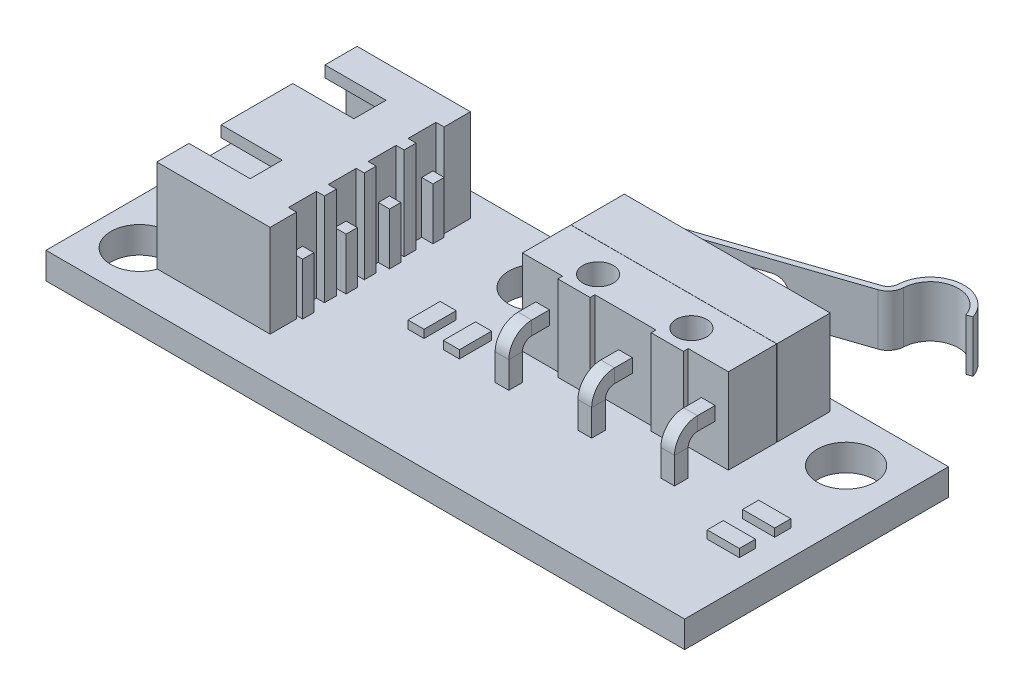
SolidWorks part; units mm, degrees
ref_plane "Front Plane" through (0, 0, 0) normal (0, 0, 1) x (1, 0, 0)
ref_plane "Top Plane" through (0, 0, 0) normal (0, 1, 0) x (1, 0, 0)
ref_plane "Right Plane" through (0, 0, 0) normal (1, 0, 0) x (0, 0, -1)
sketch "Sketch1" plane through (0, 0, 0) normal (0, 1, 0) x (1, 0, 0)
  line L1 (-19.85, -8.2) -> (19.85, -8.2)
  line L2 (-19.85, -8.2) -> (-19.85, 8.2)
  line L3 (-19.85, 8.2) -> (19.85, 8.2)
  line L4 (19.85, -8.2) -> (19.85, 8.2)
  line L5 (-19.85, -8.2) -> (19.85, 8.2) construction
  line L6 (-19.85, 8.2) -> (19.85, -8.2) construction
  point P0 (0, 0)
  dimension "D1" = 39.7
  dimension "D2" = 16.4
extrude "Boss-Extrude1" add sketch "Sketch1" along normal blind 1.65
sketch "Sketch2" plane through (0, 1.65, 0) normal (0, 1, 0) x (1, 0, 0)
  line L0 (19.85, -8.2) -> (19.85, 8.2) construction
  line L1 (13.2, 7.5) -> (0.4, 7.5)
  line L2 (13.2, 7.5) -> (13.2, 0.87)
  line L3 (13.2, 0.87) -> (0.4, 0.87)
  line L4 (0.4, 7.5) -> (0.4, 0.87)
  line L5 (19.85, 8.2) -> (-19.85, 8.2) construction
  dimension "D1" = 6.65
  dimension "D2" = 12.8
  dimension "D3" = 0.7
  dimension "D4" = 6.63
extrude "Boss-Extrude2" add sketch "Sketch2" along normal blind 5.3
sketch "Sketch3" plane through (0, 6.95, 0) normal (0, 1, 0) x (1, 0, 0)
  line L0 (0.4, 0.87) -> (13.2, 0.87) construction
  line L1 (0.4, 0.87) -> (2.9, 0.87)
  line L2 (0.4, 0.87) -> (0.4, 1.17)
  line L3 (0.4, 1.17) -> (2.9, 1.17)
  line L4 (2.9, 0.87) -> (2.9, 1.17)
  line L5 (4.9, 0.87) -> (8.7, 0.87)
  line L6 (4.9, 0.87) -> (4.9, 1.17)
  line L7 (4.9, 1.17) -> (8.7, 1.17)
  line L8 (8.7, 0.87) -> (8.7, 1.17)
  line L9 (0.4, 7.5) -> (0.4, 0.87) construction
  line L10 (13.2, 0.87) -> (10.7, 0.87)
  line L11 (13.2, 0.87) -> (13.2, 1.17)
  line L12 (13.2, 1.17) -> (10.7, 1.17)
  line L13 (10.7, 0.87) -> (10.7, 1.17)
  line L14 (0.4, 4.185) -> (13.2, 4.185)
  line L15 (0.4, 4.185) -> (0.4, 4.175)
  line L16 (0.4, 4.175) -> (13.2, 4.175)
  line L17 (13.2, 4.185) -> (13.2, 4.175)
  line L18 (13.2, 0.87) -> (13.2, 7.5) construction
  point P24 (6.8, 0.87)
  point P26 (6.8, 1.17)
  dimension "D1" = 0.01
  dimension "D2" = 3.8
  dimension "D3" = 0.3
  dimension "D4" = 2
  dimension "D5" = 2
extrude "Cut-Extrude1" cut sketch "Sketch3" against normal up to surface (5.3 mm away) up to face at (0, 1.65, 0)
sketch "Sketch4" plane through (0, 6.95, 0) normal (0, 1, 0) x (1, 0, 0)
  line L0 (2.9, 0.87) -> (4.9, 0.87) construction
  line L1 (8.7, 0.87) -> (10.7, 0.87) construction
  circle A0 centre (3.9, 2.37) radius 0.95
  circle A1 centre (9.7, 2.37) radius 0.95
  point P6 (3.9, 0.87)
  point P9 (9.7, 0.87)
  dimension "D1" = 1.9
  dimension "D2" = 1.5
extrude "Cut-Extrude2" cut sketch "Sketch4" against normal up to surface (5.3 mm away) up to face at (6.8, 1.65, -5.8425)
sketch "Sketch5" plane through (0, 6.95, 0) normal (0, 1, 0) x (1, 0, 0)
  line L0 (4.4, 7.5) -> (4.4, 7.75) construction
  line L1 (13.2, 7.5) -> (0.4, 7.5) construction
  line L2 (3.65, 7.5) -> (3.65, 7.75)
  line L3 (5.15, 7.5) -> (5.15, 7.75)
  line L4 (0.4, 7.5) -> (0.4, 4.185) construction
  line L5 (13.2, 7.5) -> (0.4, 7.5) construction
  arc A0 (3.65, 7.5) -> (5.15, 7.5) centre (4.4, 7.5) ccw
  arc A1 (5.15, 7.75) -> (3.65, 7.75) centre (4.4, 7.75) ccw
  point P4 (4.4, 7.625)
  point P11 (4.4, 8.5)
  dimension "D1" = 4
  dimension "D2" = 1
  dimension "D3" = 1.5
extrude "Boss-Extrude3" add sketch "Sketch5" against normal blind 3 from offset 1.1 offset against normal yes
sketch "Sketch6" plane through (0, 6.95, 0) normal (0, 1, 0) x (1, 0, 0)
  line L0 (1.3031, 7.5) -> (12.4306, 11.2413)
  line L1 (13.2, 7.5) -> (0.4, 7.5) construction
  line L2 (13.2, 11.5) -> (16.5175, 12.6154) construction
  line L3 (13.2, 4.185) -> (13.2, 7.5) construction
  line L5 (1.3031, 7.5) -> (0.8291, 7.3407)
  arc A0 (16.5175, 12.6154) -> (13.1108, 12.1414) centre (14.8588, 12.0577) ccw
  arc A1 (5.15, 7.75) -> (3.65, 7.75) centre (4.4, 7.75) ccw construction
  arc A2 (12.4306, 11.2413) -> (13.1108, 12.1414) centre (12.1119, 12.1892) ccw
  dimension "D2" = 1.75
  dimension "D3" = 1
  dimension "D1" = 4
  dimension "D4" = 0.5
extrude "Extrude-Thin1" add sketch "Sketch6" against normal blind 3.2 from offset 1 separate body thin thin type one direction wall 0.35 offset against normal yes
sketch "Sketch7" plane through (0, 1.65, 0) normal (0, 1, 0) x (1, 0, 0)
  line L0 (-19.85, -8.2) -> (19.85, -8.2) construction
  line L1 (-15.41, 6.7) -> (-8.37, 6.7)
  line L2 (-15.41, 6.7) -> (-15.41, -5.75)
  line L3 (-15.41, -5.75) -> (-8.37, -5.75)
  line L4 (-8.37, 6.7) -> (-8.37, -5.75)
  line L6 (-19.85, 8.2) -> (-19.85, -8.2) construction
  dimension "D1" = 2.45
  dimension "D2" = 12.45
  dimension "D3" = 7.04
  dimension "D4" = 4.44
extrude "Boss-Extrude4" add sketch "Sketch7" along normal blind 5.75
sketch "Sketch8" plane through (0, 0, 0) normal (0, -1, 0) x (1, 0, 0)
  line L0 (19.85, 8.2) -> (19.85, -8.2) construction
  line L1 (19.85, -8.2) -> (-19.85, -8.2) construction
  line L2 (-19.85, -8.2) -> (-19.85, 8.2) construction
  circle A0 centre (16.6125, -5.0725) radius 1.7875
  circle A1 centre (-2.5625, -5.0725) radius 1.7875
  circle A2 centre (-17.0625, -5.6125) radius 1.7875
  circle A3 centre (-17.0625, 5.1625) radius 1.7875
  point P8 (16.6125, -6.86)
  point P9 (18.4, -5.0725)
  point P10 (-2.5625, -6.86)
  point P11 (-4.35, -5.0725)
  point P12 (-17.0625, -7.4)
  point P13 (-18.85, -5.6125)
  point P14 (-18.85, 5.1625)
  point P15 (-17.0625, 6.95)
  point P20 (14.825, -5.0725)
  point P21 (-0.775, -5.0725)
  point P24 (-17.0625, 3.375)
  point P25 (-17.0625, -3.825)
  dimension "D1" = 3.575
  dimension "D2" = 1.45
  dimension "D3" = 1.34
  dimension "D4" = 15.6
  dimension "D5" = 0.8
  dimension "D6" = 1
  dimension "D7" = 7.2
extrude "Cut-Extrude3" cut sketch "Sketch8" against normal up to surface (1.65 mm away) up to face at (6.8, 1.65, -1.5708)
sketch "Sketch10" plane through (-15.41, 0, 0) normal (-1, 0, 0) x (0, 0, 1)
  line L0 (5.75, 7.4) -> (5.75, 1.65) construction
  line L1 (-6, 2.35) -> (5.05, 2.35)
  line L2 (-6, 2.35) -> (-6, 6.7)
  line L3 (-6, 6.7) -> (5.05, 6.7)
  line L4 (5.05, 2.35) -> (5.05, 6.7)
  line L5 (-6, 2.35) -> (5.05, 6.7) construction
  line L6 (-6, 6.7) -> (5.05, 2.35) construction
  line L7 (-6.7, 7.4) -> (5.75, 7.4) construction
  line L8 (-6.7, 7.4) -> (-6.7, 1.65) construction
  point P0 (-0.475, 4.525)
  point P9 (-0.475, 7.4)
  point P12 (-6.7, 4.525)
  dimension "D1" = 0.7
  dimension "D2" = 0.7
extrude "Cut-Extrude4" cut sketch "Sketch10" against normal offset from surface (6.04 mm away) 1 up to face at (-8.37, 4.525, -0.475)
sketch "Sketch11" plane through (0, 7.4, 0) normal (0, 1, 0) x (1, 0, 0)
  line L0 (-15.41, 4.931) -> (-15.41, -4.481) construction
  line L1 (-15.41, 4.7) -> (-11.61, 4.7)
  line L2 (-15.41, 4.7) -> (-15.41, 2.7)
  line L3 (-15.41, 2.7) -> (-11.61, 2.7)
  line L4 (-11.61, 4.7) -> (-11.61, 2.7)
  line L5 (-15.3743, -5.75) -> (-8.37, -5.75) construction
  line L6 (-15.41, -1.75) -> (-11.61, -1.75)
  line L7 (-15.41, -1.75) -> (-15.41, -3.75)
  line L8 (-15.41, -3.75) -> (-11.61, -3.75)
  line L9 (-11.61, -1.75) -> (-11.61, -3.75)
  line L10 (-8.37, 6.7) -> (-15.41, 6.7) construction
  dimension "D1" = 2
  dimension "D2" = 2
  dimension "D3" = 2
  dimension "D4" = 3.8
extrude "Cut-Extrude5" cut sketch "Sketch11" against normal up to next (0.7 mm away)
sketch "Sketch12" plane through (-9.37, 0, 0) normal (-1, 0, 0) x (0, 0, 1)
  line L0 (-6, 4.525) -> (5.05, 4.525) construction
  line L1 (-4.875, 4.875) -> (-4.175, 4.875)
  line L2 (-4.875, 4.875) -> (-4.875, 4.175)
  line L3 (-4.875, 4.175) -> (-4.175, 4.175)
  line L4 (-4.175, 4.875) -> (-4.175, 4.175)
  line L5 (-2.175, 4.875) -> (-1.475, 4.875)
  line L6 (-2.175, 4.875) -> (-2.175, 4.175)
  line L7 (-2.175, 4.175) -> (-1.475, 4.175)
  line L8 (-1.475, 4.875) -> (-1.475, 4.175)
  line L9 (0.525, 4.875) -> (1.225, 4.875)
  line L10 (0.525, 4.875) -> (0.525, 4.175)
  line L11 (0.525, 4.175) -> (1.225, 4.175)
  line L12 (1.225, 4.875) -> (1.225, 4.175)
  line L13 (3.225, 4.875) -> (3.925, 4.875)
  line L14 (3.225, 4.875) -> (3.225, 4.175)
  line L15 (3.225, 4.175) -> (3.925, 4.175)
  line L16 (3.925, 4.875) -> (3.925, 4.175)
  line L17 (-6, 2.35) -> (-6, 6.7) construction
  line L18 (5.05, 2.35) -> (5.05, 6.7) construction
  line L19 (-1.475, 4.875) -> (0.525, 4.875) construction
  line L20 (-0.475, 4.525) -> (-0.475, 4.875) construction
  line L21 (-2.175, 4.875) -> (-4.175, 4.875) construction
  line L22 (3.225, 4.875) -> (1.225, 4.875) construction
  point P22 (3.225, 4.525)
  dimension "D1" = 0.7
  dimension "D2" = 2
extrude "Boss-Extrude5" add sketch "Sketch12" along normal blind 4
chamfer "Chamfer1" distance 0.2 angle 45 16 edges at (-13.37, 4.875, 3.575) (-13.37, 4.525, 3.925) (-13.37, 4.175, 3.575) (-13.37, 4.525, 3.225) (-13.37, 4.875, 0.875) (-13.37, 4.525, 1.225) (-13.37, 4.175, 0.875) (-13.37, 4.525, 0.525) (-13.37, 4.875, -1.825) (-13.37, 4.525, -1.475) (-13.37, 4.175, -1.825) (-13.37, 4.525, -2.175) (-13.37, 4.875, -4.525) (-13.37, 4.525, -4.175) (-13.37, 4.175, -4.525) (-13.37, 4.525, -4.875)
sketch "Sketch14" plane through (0, 7.4, 0) normal (0, 1, 0) x (1, 0, 0)
  line L0 (-8.37, -5.75) -> (-8.37, 6.7) construction
  line L1 (-8.37, 5.06) -> (-8.87, 5.06)
  line L2 (-8.37, 5.06) -> (-8.37, 3.3225)
  line L3 (-8.37, 3.3225) -> (-8.87, 3.3225)
  line L4 (-8.87, 5.06) -> (-8.87, 3.3225)
  line L5 (-15.41, -5.75) -> (-8.37, -5.75) construction
  line L6 (-8.37, 2.5825) -> (-8.87, 2.5825)
  line L7 (-8.37, 2.5825) -> (-8.37, 0.845)
  line L8 (-8.37, 0.845) -> (-8.87, 0.845)
  line L9 (-8.87, 2.5825) -> (-8.87, 0.845)
  line L10 (-8.37, 0.105) -> (-8.87, 0.105)
  line L11 (-8.37, 0.105) -> (-8.37, -1.6325)
  line L12 (-8.37, -1.6325) -> (-8.87, -1.6325)
  line L13 (-8.87, 0.105) -> (-8.87, -1.6325)
  line L14 (-8.37, -2.3725) -> (-8.87, -2.3725)
  line L15 (-8.37, -2.3725) -> (-8.37, -4.11)
  line L16 (-8.37, -4.11) -> (-8.87, -4.11)
  line L17 (-8.87, -2.3725) -> (-8.87, -4.11)
  line L18 (-8.37, 6.7) -> (-15.41, 6.7) construction
  dimension "D1" = 1.64
  dimension "D2" = 1.64
  dimension "D3" = 0.74
  dimension "D4" = 0.74
  dimension "D5" = 0.74
  dimension "D6" = 0.5
extrude "Cut-Extrude6" cut sketch "Sketch14" against normal up to surface (5.75 mm away) up to face at (-2.5625, 1.65, -6.86)
sketch "Sketch16" plane through (0, 0, -1.17) normal (0, 0, 1) x (1, 0, 0)
  line L0 (0.4, 4.3) -> (1.225, 4.3) construction
  line L1 (1.225, 4.725) -> (2.075, 4.725)
  line L2 (1.225, 4.725) -> (1.225, 3.875)
  line L3 (1.225, 3.875) -> (2.075, 3.875)
  line L4 (2.075, 4.725) -> (2.075, 3.875)
  line L5 (6.375, 4.725) -> (7.225, 4.725)
  line L6 (6.375, 4.725) -> (6.375, 3.875)
  line L7 (6.375, 3.875) -> (7.225, 3.875)
  line L8 (7.225, 4.725) -> (7.225, 3.875)
  line L9 (11.525, 4.725) -> (12.375, 4.725)
  line L10 (11.525, 4.725) -> (11.525, 3.875)
  line L11 (11.525, 3.875) -> (12.375, 3.875)
  line L12 (12.375, 4.725) -> (12.375, 3.875)
  line L13 (0.4, 1.65) -> (0.4, 6.95) construction
  line L14 (1.65, 4.725) -> (1.65, 6.95) construction
  line L15 (2.9, 6.95) -> (0.4, 6.95) construction
  line L16 (11.95, 4.725) -> (11.95, 6.95) construction
  line L17 (13.2, 6.95) -> (10.7, 6.95) construction
  line L18 (6.8, 4.725) -> (6.8, 6.95) construction
  line L19 (8.7, 6.95) -> (4.9, 6.95) construction
  point P20 (6.375, 4.3)
  point P21 (11.525, 4.3)
  dimension "D1" = 0.85
sketch "Sketch17" plane through (2.9, 0, 0) normal (-1, 0, 0) x (0, 0, 1)
  line L0 (-1.17, 4.3) -> (-0.07, 4.3)
  line L1 (-1.17, 4.725) -> (-1.17, 3.875) construction
  line L2 (0.93, 3.3) -> (0.93, 1.65)
  line L3 (8.2, 1.65) -> (-8.2, 1.65) construction
  arc A0 (-0.07, 4.3) -> (0.93, 3.3) centre (-0.07, 3.3) cw
  point P9 (0.93, 4.3)
  dimension "D2" = 1
  dimension "D1" = 2.1
sweep "Sweep1" add profiles "Sketch16" path "Sketch17"
sketch "Sketch18" plane through (-2.2447, 0, -6.6764) normal (-0.3187, 0, -0.9479) x (-0.9479, 0, 0.3187)
  line L0 (-3.1253, 4.35) -> (-10.1253, 4.35) construction
  line L1 (-3.1253, 2.75) -> (-3.1253, 5.95) construction
  line L2 (-3.1253, 3.5) -> (-10.1253, 3.5)
  line L3 (-3.1253, 5.2) -> (-10.1253, 5.2)
  line L4 (-3.1253, 5.2) -> (-3.1253, 3.5)
  arc A1 (-10.1253, 5.2) -> (-10.1253, 3.5) centre (-10.1253, 4.35) ccw
  point P4 (-6.6, 4.35)
  dimension "D1" = 1.7
  dimension "D2" = 7
extrude "Cut-Extrude7" cut sketch "Sketch18" against normal up to surface (0.35 mm away) up to face at (6.6299, 4.35, -9.291)
sketch "Sketch19" plane through (-8.87, 0, 0) normal (1, 0, 0) x (0, 0, -1)
  line L0 (4.875, 4.875) -> (4.675, 4.675) construction
  line L1 (-3.925, 4.875) -> (-3.225, 4.875)
  line L2 (-3.925, 4.875) -> (-3.925, -2)
  line L3 (-3.925, -2) -> (-3.225, -2)
  line L4 (-3.225, 4.875) -> (-3.225, -2)
  line L5 (-1.225, 4.875) -> (-0.525, 4.875)
  line L6 (-1.225, 4.875) -> (-1.225, -2)
  line L7 (-1.225, -2) -> (-0.525, -2)
  line L8 (-0.525, 4.875) -> (-0.525, -2)
  line L9 (1.475, 4.875) -> (2.175, 4.875)
  line L10 (1.475, 4.875) -> (1.475, -2)
  line L11 (1.475, -2) -> (2.175, -2)
  line L12 (2.175, 4.875) -> (2.175, -2)
  line L13 (4.175, 4.875) -> (4.875, 4.875)
  line L14 (4.175, 4.875) -> (4.175, -2)
  line L15 (4.175, -2) -> (4.875, -2)
  line L16 (4.875, 4.875) -> (4.875, -2)
  line L17 (4.875, 4.875) -> (4.875, 4.175) construction
  line L18 (2.175, 4.875) -> (2.175, 4.175) construction
  line L19 (1.475, 4.875) -> (2.175, 4.875) construction
  line L20 (-0.525, 4.875) -> (-0.525, 4.175) construction
  line L21 (-0.525, 4.875) -> (-0.725, 4.675) construction
  line L22 (-3.225, 4.875) -> (-3.225, 4.175) construction
  line L23 (-3.225, 4.875) -> (-3.425, 4.675) construction
  line L24 (-6.95, 0) -> (-3.375, 0) construction
  dimension "D1" = 2
extrude "Boss-Extrude6" add sketch "Sketch19" along normal blind 0.7
sketch "Sketch20" plane through (0, 0, 0) normal (0, -1, 0) x (1, 0, 0)
  line L1 (1.225, 1.355) -> (2.075, 1.355)
  line L2 (1.225, 1.355) -> (1.225, 0.505)
  line L3 (1.225, 0.505) -> (2.075, 0.505)
  line L4 (2.075, 1.355) -> (2.075, 0.505)
  line L5 (6.375, 1.355) -> (7.225, 1.355)
  line L6 (6.375, 1.355) -> (6.375, 0.505)
  line L7 (6.375, 0.505) -> (7.225, 0.505)
  line L8 (7.225, 1.355) -> (7.225, 0.505)
  line L9 (11.525, 1.355) -> (12.375, 1.355)
  line L10 (11.525, 1.355) -> (11.525, 0.505)
  line L11 (11.525, 0.505) -> (12.375, 0.505)
  line L12 (12.375, 1.355) -> (12.375, 0.505)
extrude "Boss-Extrude7" add sketch "Sketch20" along normal blind 1.6
chamfer "Chamfer2" distance 0.2 angle 45 28 edges at (11.95, -1.6, 1.355) (12.375, -1.6, 0.93) (11.95, -1.6, 0.505) (11.525, -1.6, 0.93) (6.8, -1.6, 1.355) (7.225, -1.6, 0.93) (6.8, -1.6, 0.505) (6.375, -1.6, 0.93) (1.65, -1.6, 1.355) (2.075, -1.6, 0.93) (1.65, -1.6, 0.505) (1.225, -1.6, 0.93) (-8.52, -2, -4.175) (-8.17, -2, -4.525) (-8.52, -2, -4.875) (-8.87, -2, -4.525) (-8.52, -2, -1.475) (-8.17, -2, -1.825) (-8.52, -2, -2.175) (-8.87, -2, -1.825) (-8.52, -2, 1.225) (-8.17, -2, 0.875) (-8.52, -2, 0.525) (-8.87, -2, 0.875) (-8.52, -2, 3.925) (-8.17, -2, 3.575) (-8.52, -2, 3.225) (-8.87, -2, 3.575)
sketch "Sketch21" plane through (0, 1.65, 0) normal (0, 1, 0) x (1, 0, 0)
  line L0 (-19.85, -8.2) -> (19.85, -8.2) construction
  line L1 (19.85, -8.2) -> (19.85, 8.2) construction
  line L3 (16.25, -1) -> (18.25, -1)
  line L4 (16.25, -1) -> (16.25, 0)
  line L5 (16.25, -2.2) -> (18.25, -2.2)
  line L6 (16.25, -2.2) -> (16.25, -3.2)
  line L7 (16.25, -3.2) -> (18.25, -3.2)
  line L8 (18.25, -2.2) -> (18.25, -3.2)
  line L9 (-4.35, 0.8) -> (-3.35, 0.8)
  line L10 (-4.35, 0.8) -> (-4.35, -1.2)
  line L11 (-4.35, -1.2) -> (-3.35, -1.2)
  line L12 (-3.35, 0.8) -> (-3.35, -1.2)
  line L13 (-2.15, 0.8) -> (-1.15, 0.8)
  line L14 (-2.15, 0.8) -> (-2.15, -1.2)
  line L15 (-2.15, -1.2) -> (-1.15, -1.2)
  line L16 (-1.15, 0.8) -> (-1.15, -1.2)
  line L17 (16.25, 0) -> (18.25, 0)
  line L18 (18.25, -1) -> (18.25, 0)
  dimension "D1" = 5
  dimension "D2" = 2
  dimension "D3" = 1
  dimension "D4" = 1.6
  dimension "D5" = 1.2
  dimension "D6" = 2
  dimension "D7" = 1
  dimension "D8" = 1.2
  dimension "D9" = 21
  dimension "D10" = 7
extrude "Boss-Extrude8" add sketch "Sketch21" along normal blind 0.5
